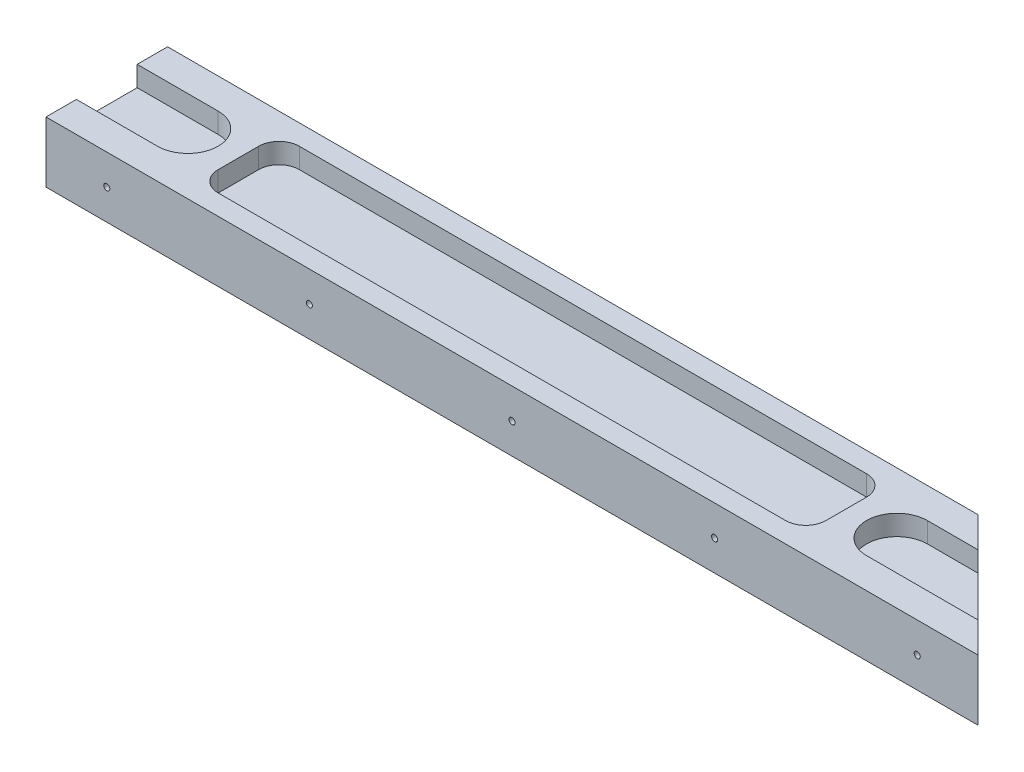
SolidWorks part; units mm, degrees
ref_plane "Front Plane" through (0, 0, 0) normal (0, 0, 1) x (1, 0, 0)
ref_plane "Top Plane" through (0, 0, 0) normal (0, 1, 0) x (1, 0, 0)
ref_plane "Right Plane" through (0, 0, 0) normal (1, 0, 0) x (0, 0, -1)
sketch "Sketch1" plane through (0, 0, 0) normal (0, 1, 0) x (1, 0, 0)
  line L0 (0, 0) -> (230, 0)
  line L1 (230, 0) -> (200, 30)
  line L2 (200, 30) -> (0, 30)
  line L3 (0, 30) -> (0, 0)
  dimension "D1" = 230
  dimension "D2" = 200
  dimension "D3" = 30
extrude "Boss-Extrude1" add sketch "Sketch1" along normal blind 15
sketch "Sketch2" plane through (0, 15, 0) normal (0, 1, 0) x (1, 0, 0)
  line L0 (-20, 15) -> (20, 15) construction
  line L1 (-20, 22.5) -> (20, 22.5)
  line L2 (-20, 7.5) -> (20, 7.5)
  line L3 (0, 30) -> (0, 0) construction
  line L4 (0, 15) -> (215, 15) construction
  line L5 (230, 0) -> (200, 30) construction
  line L6 (107.5, 15) -> (107.5, 30) construction
  line L7 (200, 30) -> (0, 30) construction
  line L8 (235, 15) -> (195, 15) construction
  line L9 (235, 22.5) -> (195, 22.5)
  line L10 (235, 7.5) -> (195, 7.5)
  arc A0 (-20, 22.5) -> (-20, 7.5) centre (-20, 15) ccw
  arc A1 (20, 7.5) -> (20, 22.5) centre (20, 15) ccw
  arc A2 (235, 22.5) -> (235, 7.5) centre (235, 15) cw
  arc A3 (195, 7.5) -> (195, 22.5) centre (195, 15) cw
  point P2 (0, 15)
  point P9 (0, 15)
  point P20 (215, 15)
  dimension "D1" = 40
  dimension "D2" = 15
extrude "Cut-Extrude1" cut sketch "Sketch2" against normal blind 5
sketch "Sketch3" plane through (0, 0, 0) normal (0, -1, 0) x (1, 0, 0)
  line L0 (195, -7.5) -> (222.5, -7.5) construction
  line L1 (230, 0) -> (200, -30) construction
  line L2 (207.5, -22.5) -> (195, -22.5) construction
  line L3 (0, -30) -> (0, 0) construction
  line L4 (20, -22.5) -> (0, -22.5) construction
  line L5 (0, -7.5) -> (20, -7.5) construction
  line L6 (195, -7.5) -> (222.5, -7.5)
  line L7 (222.5, -7.5) -> (207.5, -22.5)
  line L8 (207.5, -22.5) -> (195, -22.5)
  line L9 (0, -22.5) -> (0, -7.5)
  line L10 (20, -22.5) -> (0, -22.5)
  line L11 (0, -7.5) -> (20, -7.5)
  arc A0 (195, -7.5) -> (195, -22.5) centre (195, -15) ccw construction
  arc A1 (20, -22.5) -> (20, -7.5) centre (20, -15) ccw construction
  arc A2 (195, -7.5) -> (195, -22.5) centre (195, -15) ccw
  arc A3 (20, -22.5) -> (20, -7.5) centre (20, -15) ccw
extrude "Cut-Extrude2" cut sketch "Sketch3" against normal blind 5
sketch "Sketch4" plane through (0, 0, 0) normal (0, 0, 1) x (1, 0, 0)
  line L0 (0, 7.5) -> (230, 7.5) construction
  line L1 (0, 15) -> (0, 0) construction
  line L2 (230, 15) -> (230, 0) construction
  circle A0 centre (115, 7.5) radius 0.75
  circle A1 centre (165, 7.5) radius 0.75
  circle A2 centre (215, 7.5) radius 0.75
  circle A3 centre (65, 7.5) radius 0.75
  circle A4 centre (15, 7.5) radius 0.75
  dimension "D1" = 1.5
  dimension "D2" = 3
  dimension "D3" = 3
extrude "Cut-Extrude3" cut sketch "Sketch4" against normal up to surface (30 mm away) up to face at (100, 7.5, -30)
sketch "Sketch5" plane through (0, 15, 0) normal (0, 1, 0) x (1, 0, 0)
  line L0 (200, 30) -> (0, 30) construction
  line L1 (37.5, 25) -> (177.5, 25)
  line L2 (32.5, 20) -> (32.5, 10)
  line L3 (37.5, 5) -> (177.5, 5)
  line L4 (182.5, 20) -> (182.5, 10)
  line L5 (0, 0) -> (230, 0) construction
  arc A0 (20, 7.5) -> (20, 22.5) centre (20, 15) ccw construction
  arc A1 (195, 22.5) -> (195, 7.5) centre (195, 15) ccw construction
  arc A2 (177.5, 25) -> (182.5, 20) centre (177.5, 20) cw
  arc A3 (177.5, 5) -> (182.5, 10) centre (177.5, 10) ccw
  arc A4 (32.5, 10) -> (37.5, 5) centre (37.5, 10) ccw
  arc A5 (37.5, 25) -> (32.5, 20) centre (37.5, 20) ccw
  point P4 (27.5, 15)
  point P5 (187.5, 15)
  dimension "D5" = 5
  dimension "D1" = 5
  dimension "D2" = 5
  dimension "D3" = 5
  dimension "D4" = 5
extrude "Cut-Extrude4" cut sketch "Sketch5" against normal blind 5
